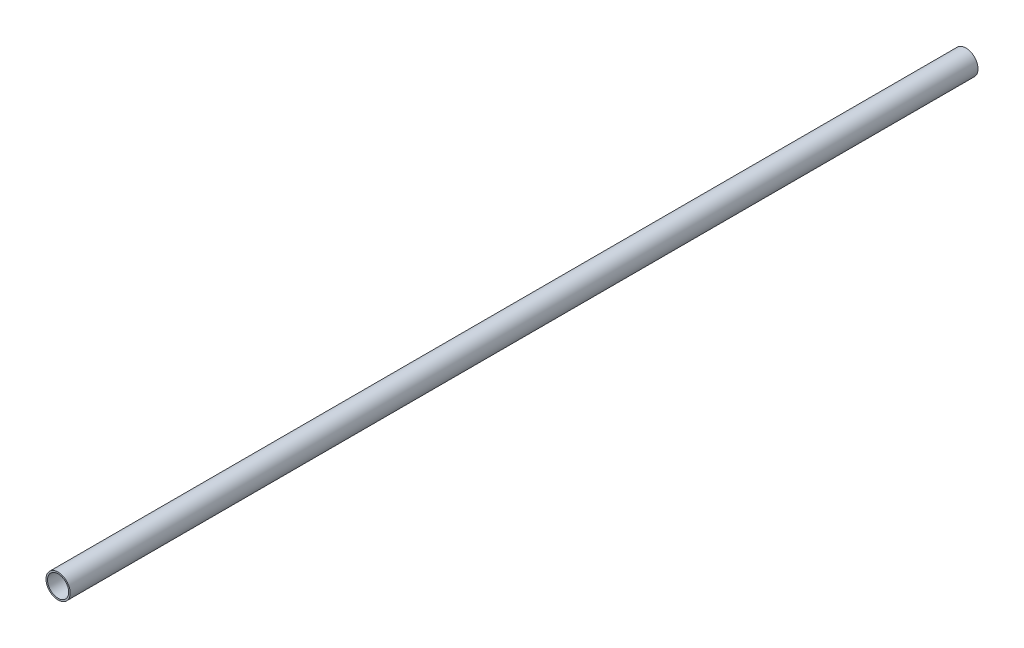
SolidWorks part; units mm, degrees
material "1060-H12 Rod (SS)"
ref_plane "Front Plane" through (0, 0, 0) normal (0, 0, 1) x (1, 0, 0)
ref_plane "Top Plane" through (0, 0, 0) normal (0, 1, 0) x (1, 0, 0)
ref_plane "Right Plane" through (0, 0, 0) normal (1, 0, 0) x (0, 0, -1)
sketch "Sketch1" plane through (0, 0, 0) normal (0, 0, 1) x (1, 0, 0)
  circle A0 centre (0, 0) radius 4
  circle A1 centre (0, 0) radius 3.5
  dimension "D1" = 8
  dimension "D2" = 7
extrude "Boss-Extrude1" add sketch "Sketch1" along normal blind 300
